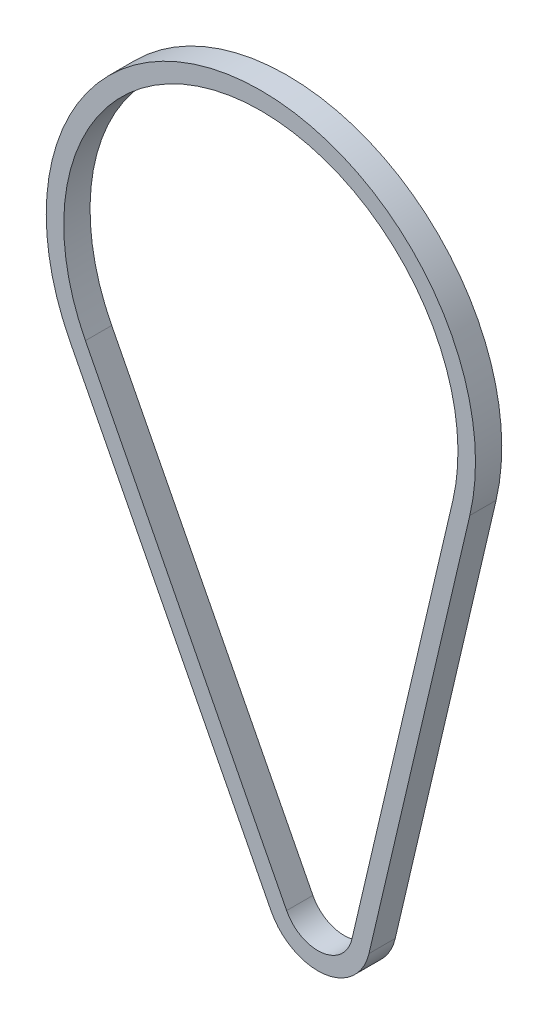
SolidWorks part; units mm, degrees
ref_plane "Plano frontal" through (0, 0, 0) normal (0, 0, 1) x (1, 0, 0)
ref_plane "Plano superior" through (0, 0, 0) normal (0, 1, 0) x (1, 0, 0)
ref_plane "Plano direito" through (0, 0, 0) normal (1, 0, 0) x (0, 0, -1)
sketch "Esboço2" plane through (0, 0, 0) normal (0, 0, 1) x (1, 0, 0)
  line L0 (0, 0) -> (1, 0) construction
  line L1 (0, 0) -> (0, 1) construction
  line L2 (-17.8025, -9.1144) -> (-132.6388, 215.1864)
  line L3 (77.0263, 240.7597) -> (19.4713, -4.5681)
  arc A0 (19.4713, -4.5681) -> (-17.8025, -9.1144) centre (0, 0) cw
  arc A1 (-132.6388, 215.1864) -> (77.0263, 240.7597) centre (-32.5, 266.455) cw
extrude "Extrusão-Fina1" add sketch "Esboço2" along normal mid plane 15 thin thin type one direction wall 10
